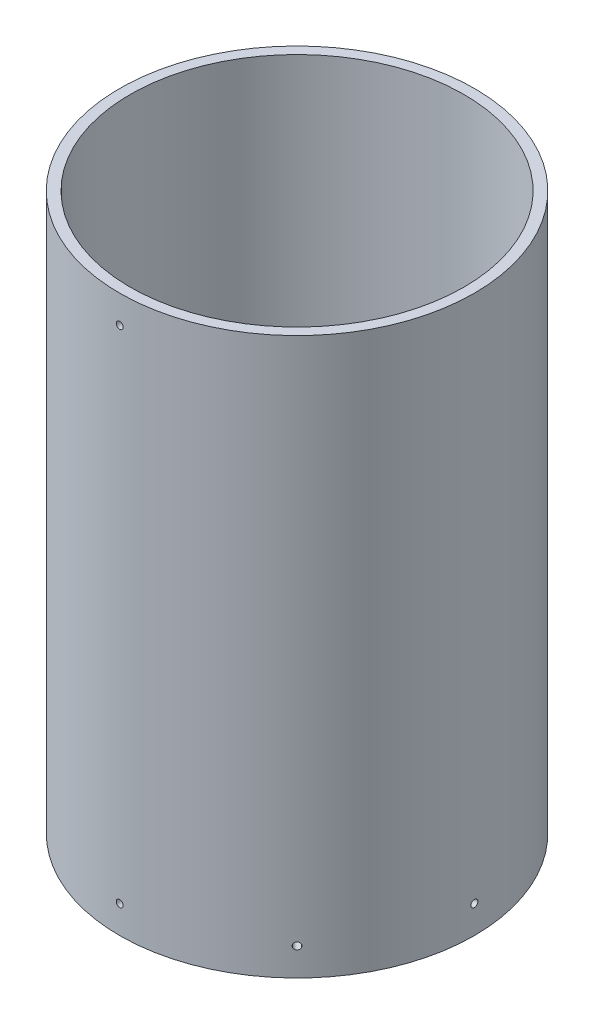
SolidWorks part; units mm, degrees
material "PVC Rigid"
ref_plane "Front Plane" through (0, 0, 0) normal (0, 0, 1) x (1, 0, 0)
ref_plane "Top Plane" through (0, 0, 0) normal (0, 1, 0) x (1, 0, 0)
ref_plane "Right Plane" through (0, 0, 0) normal (1, 0, 0) x (0, 0, -1)
sketch "Sketch1" plane through (0, 0, 0) normal (0, 0, 1) x (1, 0, 0)
  line L0 (0, 0) -> (0, -508)
  dimension "D1" = 508
other "Pipe (standard, s40) P12(2)"
ref_plane "Plane1" through (0, 0, 0) normal (0, -1, 0) x (1, 0, 0)
sketch "Sketch12" plane through (0, 0, 0) normal (0, -1, 0) x (1, 0, 0)
  circle A0 centre (0, 0) radius 152.4
  circle A1 centre (0, 0) radius 161.925
  point P3 (0, 0)
  dimension "In_dia" = 304.8
  dimension "Out_dia" = 323.85
sketch "Sketch13" plane through (0, 0, 0) normal (0, 0, 1) x (1, 0, 0)
  line L0 (0, 0) -> (0, -508) construction
  line L1 (-161.925, -508) -> (161.925, -508) construction
  line L2 (161.925, 0) -> (-161.925, 0) construction
  circle A0 centre (0, -482.6) radius 3.175
  circle A1 centre (0, -25.4) radius 3.175
  dimension "D1" = 6.35
  dimension "D2" = 25.4
  dimension "D4" = 25.4
  dimension "D3" = 2
extrude "Cut-Extrude1" cut sketch "Sketch13" along normal through all
sketch "Sketch14" plane through (0, 0, 0) normal (0, 0, 1) x (1, 0, 0)
  line L0 (0, 0) -> (0, -508) construction
  line L1 (-161.925, -508) -> (161.925, -508) construction
ref_plane "Plane2" through (0, 0, 0) normal (-0.7071, 0, -0.7071) x (0, -1, 0)
sketch "Sketch15" plane through (0, 0, 0) normal (-0.7071, 0, -0.7071) x (0, -1, 0)
  line L0 (0, 0) -> (508, 0) construction
  line L1 (508, -161.925) -> (508, 161.925) construction
  circle A0 centre (482.6, 0) radius 3.175
  dimension "D1" = 6.35
  dimension "D2" = 25.4
extrude "Cut-Extrude2" cut sketch "Sketch15" against normal through all
sketch "Sketch16" plane through (0, 0, 0) normal (1, 0, 0) x (0, 0, -1)
  line L0 (0, 0) -> (0, -508) construction
  line L1 (-161.925, -508) -> (161.925, -508) construction
  circle A0 centre (0, -482.6) radius 3.175
  dimension "D1" = 6.35
  dimension "D2" = 25.4
extrude "Cut-Extrude3" cut sketch "Sketch16" along normal through all
